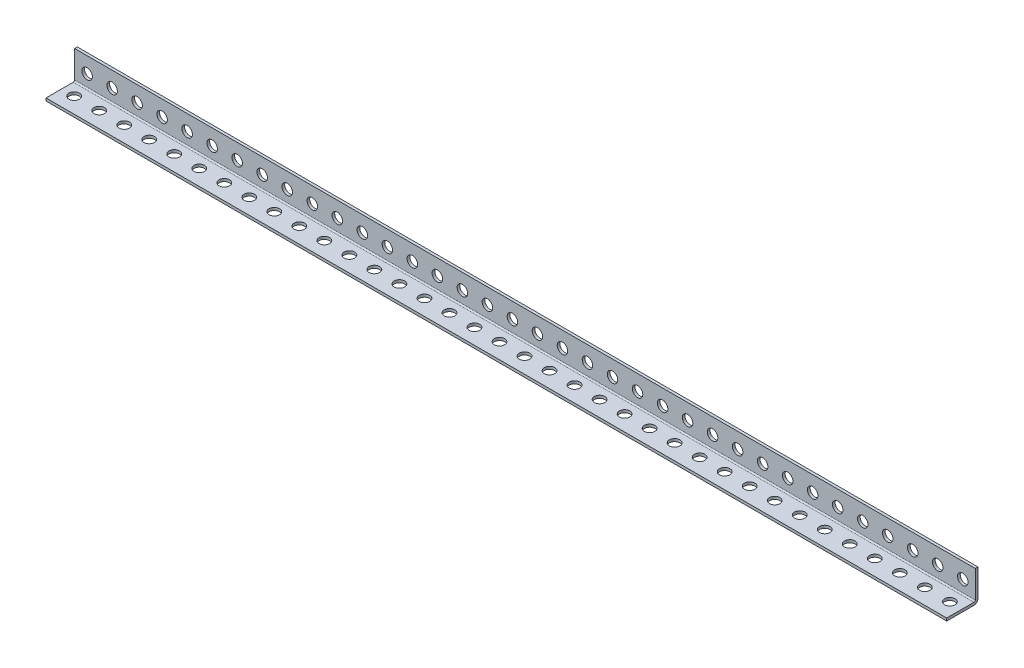
SolidWorks part; units mm, degrees
ref_plane "Front Plane" through (0, 0, 0) normal (0, 0, 1) x (1, 0, 0)
ref_plane "Top Plane" through (0, 0, 0) normal (0, 1, 0) x (1, 0, 0)
ref_plane "Right Plane" through (0, 0, 0) normal (1, 0, 0) x (0, 0, -1)
sketch "Sketch1" plane through (0, 0, 0) normal (1, 0, 0) x (0, 0, -1)
  line L0 (-15.875, -13.1318) -> (13.1318, -13.1318) construction
  line L1 (13.1318, -13.1318) -> (13.1318, 15.875) construction
  line L2 (13.1318, 15.875) -> (15.875, 15.875) construction
  line L3 (15.875, 15.875) -> (15.875, -15.875) construction
  line L4 (15.875, -15.875) -> (-15.875, -15.875) construction
  line L5 (-15.875, -15.875) -> (-15.875, -13.1318) construction
  line L6 (0, -15.875) -> (0, 15.875) construction
  line L7 (15.875, 0) -> (-15.875, 0) construction
  dimension "Thickness | T" = 2.7432
  dimension "Width (A)" = 31.75
  dimension "Width (B)" = 31.75
sketch "Sketch2" plane through (0, 0, 0) normal (0, 0, 1) x (1, 0, 0)
  line L0 (-457.2, 0) -> (457.2, 0) construction
  line L1 (-457.2, 15.875) -> (457.2, 15.875) construction
  line L2 (-457.2, 15.875) -> (-457.2, -15.875) construction
  line L3 (-457.2, -15.875) -> (457.2, -15.875) construction
  line L4 (457.2, 15.875) -> (457.2, -15.875) construction
  line L5 (0, 15.875) -> (0, -15.875) construction
  line L7 (-457.2, -13.1318) -> (457.2, -13.1318) construction
  circle A0 centre (444.5, 0) radius 5.334 construction
  circle A1 centre (419.1, 0) radius 5.334 construction
  point P15 (381, 0)
  point P16 (-381, 0)
  point P24 (449.834, 0)
  dimension "Mounting Hole Diameter" = 10.668
  dimension "Length | L" = 914.4
  dimension "Mounting Hole Center to Center" = 25.4
  dimension "D1" = 12.7
  dimension "D2" = 63.5
sketch "Sketch3" plane through (0, 0, 0) normal (0, 1, 0) x (1, 0, 0)
  line L1 (-457.2, 15.875) -> (457.2, 15.875) construction
  line L2 (-457.2, 15.875) -> (-457.2, -15.875) construction
  line L3 (-457.2, -15.875) -> (457.2, -15.875) construction
  line L4 (457.2, 15.875) -> (457.2, -15.875) construction
  line L5 (-457.2, 13.1318) -> (457.2, 13.1318) construction
  line L7 (-457.2, 0) -> (457.2, 0) construction
  circle A0 centre (444.5, 0) radius 5.334 construction
  circle A1 centre (419.1, 0) radius 5.334 construction
  point P19 (-381, 0)
  point P21 (449.834, 0)
  point P22 (381, 0)
sketch "Sketch4" plane through (0, 0, 0) normal (1, 0, 0) x (0, 0, -1)
  line L0 (-15.875, -13.1318) -> (11.7602, -13.1318)
  line L1 (13.1318, -11.7602) -> (13.1318, 15.875)
  line L2 (13.1318, 15.875) -> (15.875, 15.875)
  line L3 (15.875, 15.875) -> (15.875, -11.7602)
  line L4 (11.7602, -15.875) -> (-15.875, -15.875)
  line L5 (-15.875, -15.875) -> (-15.875, -13.1318)
  line L6 (11.7602, -13.1318) -> (11.7602, -10.3886) construction
  arc A0 (11.7602, -13.1318) -> (13.1318, -11.7602) centre (11.7602, -11.7602) ccw
  arc A1 (15.875, -11.7602) -> (11.7602, -15.875) centre (11.7602, -11.7602) cw
extrude "Boss-Extrude1" add sketch "Sketch4" along normal up to vertex (457.2 mm away) and the other way up to vertex (457.2 mm away) up to point (457.2, 0, 0) other way up to point (-457.2, 0, 0)
sketch "Sketch5" plane through (0, 0, 0) normal (0, 0, 1) x (1, 0, 0)
  circle A0 centre (444.5, 0) radius 5.334
extrude "Cut-Extrude1" cut sketch "Sketch5" against normal through all
sketch "Sketch6" plane through (0, 0, 0) normal (0, 1, 0) x (1, 0, 0)
  circle A0 centre (444.5, 0) radius 5.334
extrude "Cut-Extrude2" cut sketch "Sketch6" against normal through all
pattern_linear "LPattern1" count 36 spacing 25.4 along (-1, 0, 0) of "Cut-Extrude2", "Cut-Extrude1"
equation "\"D1@Sketch2\"= ( \"Length | L@Sketch2\" - \"Mounting Hole Center to Center@Sketch2\" * \"Num Holes\" ) / 2"
equation "\"Num Holes\"= int ( \"Length | L@Sketch2\" / \"Mounting Hole Center to Center@Sketch2\" ) - 1"
equation "\"D2@Sketch2\"=\"Mounting Hole Center to Center@Sketch2\"*2.5"
equation "\"D3@LPattern1\"=\"Mounting Hole Center to Center@Sketch2\""
